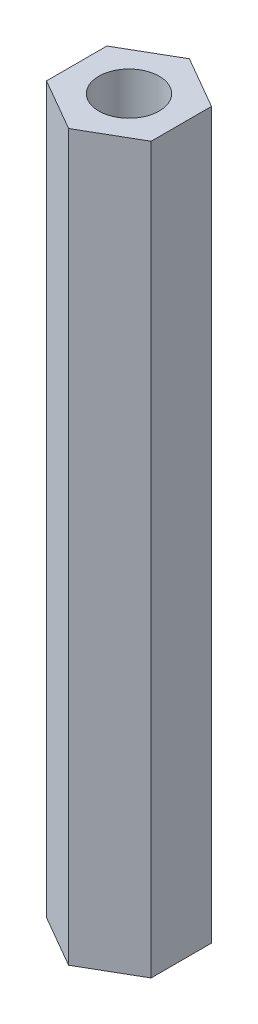
SolidWorks part; units mm, degrees
ref_plane "Face" through (0, 0, 0) normal (0, 0, 1) x (1, 0, 0)
ref_plane "Dessus" through (0, 0, 0) normal (0, 1, 0) x (1, 0, 0)
ref_plane "Droite" through (0, 0, 0) normal (1, 0, 0) x (0, 0, -1)
sketch "Esquisse1" plane through (0, 0, 0) normal (0, 1, 0) x (1, 0, 0)
  line L0 (0, 0) -> (0, 5.5688) construction
  line L1 (0, 5) -> (-4.3301, 2.5)
  line L2 (-4.3301, 2.5) -> (-4.3301, -2.5)
  line L3 (-4.3301, -2.5) -> (0, -5)
  line L4 (0, -5) -> (4.3301, -2.5)
  line L5 (4.3301, -2.5) -> (4.3301, 2.5)
  line L6 (4.3301, 2.5) -> (0, 5)
  circle A0 centre (0, 0) radius 4.3301 construction
  circle A1 centre (0, 0) radius 2.5
  dimension "D1" = 10
  dimension "D2" = 5
extrude "Extrusion1" add sketch "Esquisse1" along normal blind 60
